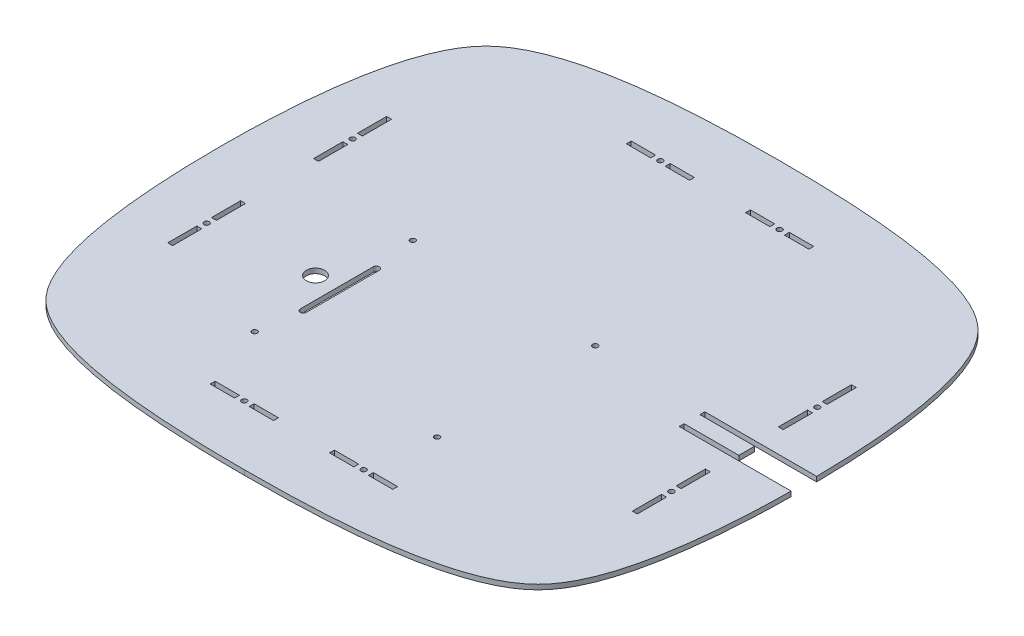
SolidWorks part; units mm, degrees
ref_plane "Front Plane" through (0, 0, 0) normal (0, 0, 1) x (1, 0, 0)
ref_plane "Top Plane" through (0, 0, 0) normal (0, 1, 0) x (1, 0, 0)
ref_plane "Right Plane" through (0, 0, 0) normal (1, 0, 0) x (0, 0, -1)
sketch "Sketch1" plane through (0, 0, 0) normal (0, 1, 0) x (1, 0, 0)
  line L0 (0, 0) -> (0, 220) construction
  line L1 (0, 220) -> (-240, 220) construction
  line L2 (-240, 220) -> (-240, 0) construction
  line L3 (-240, 0) -> (0, 0) construction
  spline S0 degree 3 poles (0, 220) (-73.455, 220) (-164.2067, 213.7234) (-232.0827, 156.7761) (-240, 64.8705) (-240, 0) knots 0 0 0 0 0.467314 0.567314 1 1 1 1
  spline S1 degree 3 poles (0, 220) (73.455, 220) (164.2067, 213.7234) (232.0827, 156.7761) (240, 64.8705) (240, 0) knots 0 0 0 0 0.467314 0.567314 1 1 1 1
  spline S2 degree 3 poles (0, -220) (73.455, -220) (164.2067, -213.7234) (232.0827, -156.7761) (240, -64.8705) (240, 0) knots 0 0 0 0 0.467314 0.567314 1 1 1 1
  spline S3 degree 3 poles (0, -220) (-73.455, -220) (-164.2067, -213.7234) (-232.0827, -156.7761) (-240, -64.8705) (-240, 0) knots 0 0 0 0 0.467314 0.567314 1 1 1 1
  dimension "D1" = 240
  dimension "D2" = 220
extrude "Boss-Extrude1" add sketch "Sketch1" along normal blind 4
sketch "Sketch2" plane through (0, 4, 0) normal (0, 1, 0) x (1, 0, 0)
  line L0 (0, 200) -> (0, -200) construction
  line L1 (0, 8.5) -> (239.1667, 8.5) construction
  line L2 (148, -6.5) -> (240, -10.5) construction
  line L3 (-240, 0) -> (240, 0) construction
  line L4 (148, 10.5) -> (240, 10.5)
  line L5 (148, 10.5) -> (148, 6.5)
  line L6 (-189, 200) -> (-189, -200) construction
  line L7 (-220, -169) -> (220, -169) construction
  line L8 (-189, 90) -> (-193, 90)
  line L9 (-189, 90) -> (-189, 66)
  line L10 (-189, 66) -> (-193, 66)
  line L11 (-193, 90) -> (-193, 66)
  line L12 (-189, 54) -> (-193, 54)
  line L13 (-189, 54) -> (-189, 30)
  line L14 (-189, 30) -> (-193, 30)
  line L15 (-193, 54) -> (-193, 30)
  line L16 (-189, -30) -> (-193, -30)
  line L17 (-189, -30) -> (-189, -54)
  line L18 (-189, -54) -> (-193, -54)
  line L19 (-193, -30) -> (-193, -54)
  line L20 (-189, -66) -> (-193, -66)
  line L21 (-189, -66) -> (-189, -90)
  line L22 (-189, -90) -> (-193, -90)
  line L23 (-193, -66) -> (-193, -90)
  line L24 (75, 169) -> (75, 173)
  line L25 (-75, -169) -> (-55, -169)
  line L26 (-75, -169) -> (-75, -173)
  line L27 (-75, -173) -> (-55, -173)
  line L28 (-55, -169) -> (-55, -173)
  line L29 (-43, -169) -> (-23, -169)
  line L30 (-43, -169) -> (-43, -173)
  line L31 (-43, -173) -> (-23, -173)
  line L32 (-23, -169) -> (-23, -173)
  line L33 (23, -169) -> (43, -169)
  line L34 (23, -169) -> (23, -173)
  line L35 (23, -173) -> (43, -173)
  line L36 (43, -169) -> (43, -173)
  line L37 (55, -169) -> (75, -169)
  line L38 (55, -169) -> (55, -173)
  line L39 (55, -173) -> (75, -173)
  line L40 (75, -169) -> (75, -173)
  line L41 (55, 173) -> (75, 173)
  line L42 (55, 169) -> (55, 173)
  line L43 (55, 169) -> (75, 169)
  line L44 (43, 169) -> (43, 173)
  line L45 (23, 173) -> (43, 173)
  line L46 (23, 169) -> (23, 173)
  line L47 (23, 169) -> (43, 169)
  line L48 (-23, 169) -> (-23, 173)
  line L49 (-43, 173) -> (-23, 173)
  line L50 (-43, 169) -> (-43, 173)
  line L51 (-43, 169) -> (-23, 169)
  line L52 (-55, 169) -> (-55, 173)
  line L53 (-75, 173) -> (-55, 173)
  line L54 (-75, 169) -> (-75, 173)
  line L55 (-75, 169) -> (-55, 169)
  line L56 (193, -66) -> (193, -90)
  line L57 (189, -90) -> (193, -90)
  line L58 (189, -66) -> (189, -90)
  line L59 (189, -66) -> (193, -66)
  line L60 (193, -30) -> (193, -54)
  line L61 (189, -54) -> (193, -54)
  line L62 (189, -30) -> (189, -54)
  line L63 (189, -30) -> (193, -30)
  line L64 (193, 54) -> (193, 30)
  line L65 (189, 30) -> (193, 30)
  line L66 (189, 54) -> (189, 30)
  line L67 (189, 54) -> (193, 54)
  line L68 (193, 90) -> (193, 66)
  line L69 (189, 66) -> (193, 66)
  line L70 (189, 90) -> (189, 66)
  line L71 (189, 90) -> (193, 90)
  line L72 (148, 6.5) -> (193, 6.5)
  line L73 (240, 10.5) -> (240, 6.5)
  line L74 (148, 10.5) -> (240, 6.5) construction
  line L75 (148, 6.5) -> (240, 10.5) construction
  line L76 (148, -10.5) -> (240, -6.5) construction
  line L77 (240, -10.5) -> (240, -6.5)
  line L78 (148, -6.5) -> (193, -6.5)
  line L79 (148, -10.5) -> (148, -6.5)
  line L80 (148, -10.5) -> (240, -10.5)
  line L81 (193, 6.5) -> (193, -6.5)
  line L82 (240, 6.5) -> (240, -6.5)
  point P4 (194, 8.5)
  point P83 (194, -8.5)
  dimension "D1" = 189
  dimension "D2" = 12
  dimension "D3" = 24
  dimension "D4" = 24
  dimension "D5" = 24
  dimension "D6" = 12
  dimension "D7" = 24
  dimension "D8" = 4
  dimension "D9" = 30
  dimension "D10" = 30
  dimension "D11" = 169
  dimension "D12" = 12
  dimension "D13" = 20
  dimension "D14" = 20
  dimension "D15" = 4
  dimension "D16" = 23
  dimension "D17" = 20
  dimension "D18" = 12
  dimension "D19" = 20
  dimension "D20" = 23
  dimension "D21" = 148
  dimension "D22" = 4
  dimension "D23" = 6.5
extrude "Cut-Extrude1" cut sketch "Sketch2" against normal blind 6
hole_wizard "M4 Clearance Hole1" positions "Sketch4" profile "Sketch3" hole size "M4" standard "DIN"
sketch "Sketch4" plane through (0, 4, 0) normal (0, 1, 0) x (-1, 0, 0)
  line L0 (55, -171) -> (43, -171) construction
  line L1 (55, -169) -> (55, -173) construction
  line L2 (43, -173) -> (43, -169) construction
  line L3 (43, -171) -> (-43, -171) construction
  line L4 (-43, -169) -> (-43, -173) construction
  line L5 (-43, -171) -> (-55, -171) construction
  line L6 (-55, -173) -> (-55, -169) construction
  line L8 (-191, -66) -> (-191, -54) construction
  line L9 (-189, -66) -> (-193, -66) construction
  line L10 (-193, -54) -> (-189, -54) construction
  line L12 (-191, 54) -> (-191, 66) construction
  line L13 (-189, 54) -> (-193, 54) construction
  line L14 (-193, 66) -> (-189, 66) construction
  line L16 (55, 171) -> (43, 171) construction
  line L17 (55, 173) -> (55, 169) construction
  line L18 (43, 169) -> (43, 173) construction
  line L20 (-43, 171) -> (-55, 171) construction
  line L21 (-43, 173) -> (-43, 169) construction
  line L22 (-55, 169) -> (-55, 173) construction
  line L24 (191, 54) -> (191, 66) construction
  line L25 (193, 54) -> (189, 54) construction
  line L26 (189, 66) -> (193, 66) construction
  line L28 (191, -66) -> (191, -54) construction
  line L29 (193, -66) -> (189, -66) construction
  line L30 (189, -54) -> (193, -54) construction
  point P0 (49, -171)
  point P67 (-49, -171)
  point P69 (-191, -60)
  point P71 (-191, 60)
  point P73 (-49, 171)
  point P75 (49, 171)
  point P77 (191, 60)
  point P79 (191, -60)
sketch "Sketch3" plane through (-49, 4, -171) normal (1, 0, 0) x (0, 0, 1)
  line L0 (0, 0) -> (0, 7.2919)
  line L1 (0, 7.2919) -> (2.15, 6)
  line L2 (2.15, 6) -> (2.15, 0)
  line L5 (2.15, 0) -> (0, 0)
  line L10 (0, 7.2919) -> (-2.15, 6) construction
  line L11 (0, -6.35) -> (0, 107.95) construction
  dimension "Hole Dia." = 4.3
  dimension "Hole Depth" = 6
  dimension "Drill Angle" = 118
hole_wizard "M4 Clearance Hole2" positions "Sketch6" profile "Sketch5" hole size "M4" standard "DIN"
sketch "Sketch6" plane through (0, 4, 0) normal (0, 1, 0) x (-1, 0, 0)
  line L1 (94, -12.5) -> (-56, -12.5) construction
  line L2 (94, -12.5) -> (94, 117.5) construction
  line L3 (94, 117.5) -> (-56, 117.5) construction
  line L4 (-56, -12.5) -> (-56, 117.5) construction
  line L5 (23, 169) -> (43, 169) construction
  line L6 (189, 90) -> (189, 66) construction
  point P0 (94, -12.5)
  point P1 (-56, -12.5)
  point P3 (-56, 117.5)
  point P5 (94, 117.5)
  dimension "D1" = 150
  dimension "D2" = 130
  dimension "D3" = 51.5
  dimension "D4" = 95
sketch "Sketch5" plane through (-94, 4, -12.5) normal (1, 0, 0) x (0, 0, 1)
  line L0 (0, 0) -> (0, 7.2919)
  line L1 (0, 7.2919) -> (2.15, 6)
  line L2 (2.15, 6) -> (2.15, 0)
  line L5 (2.15, 0) -> (0, 0)
  line L10 (0, 7.2919) -> (-2.15, 6) construction
  line L11 (0, -6.35) -> (0, 107.95) construction
  dimension "Hole Dia." = 4.3
  dimension "Hole Depth" = 6
  dimension "Drill Angle" = 118
sketch "Sketch7" plane through (0, 4, 0) normal (0, 1, 0) x (1, 0, 0)
  line L0 (-94, 12.5) -> (-94, -117.5) construction
  line L1 (-89, -22.5) -> (-89, -82.5) construction
  line L2 (-86.5, -22.5) -> (-86.5, -82.5)
  line L3 (-91.5, -22.5) -> (-91.5, -82.5)
  line L4 (-94, -52.5) -> (-150.1312, -52.5) construction
  arc A2 (-86.5, -22.5) -> (-91.5, -22.5) centre (-89, -22.5) ccw
  arc A3 (-91.5, -82.5) -> (-86.5, -82.5) centre (-89, -82.5) ccw
  circle A4 centre (-109, -52.5) radius 7.5
  point P4 (-89, -52.5)
  dimension "D5" = 15
  dimension "D1" = 5
  dimension "D2" = 60
  dimension "D3" = 65
  dimension "D4" = 5
  dimension "D6" = 20
extrude "Cut-Extrude2" cut sketch "Sketch7" against normal blind 10
